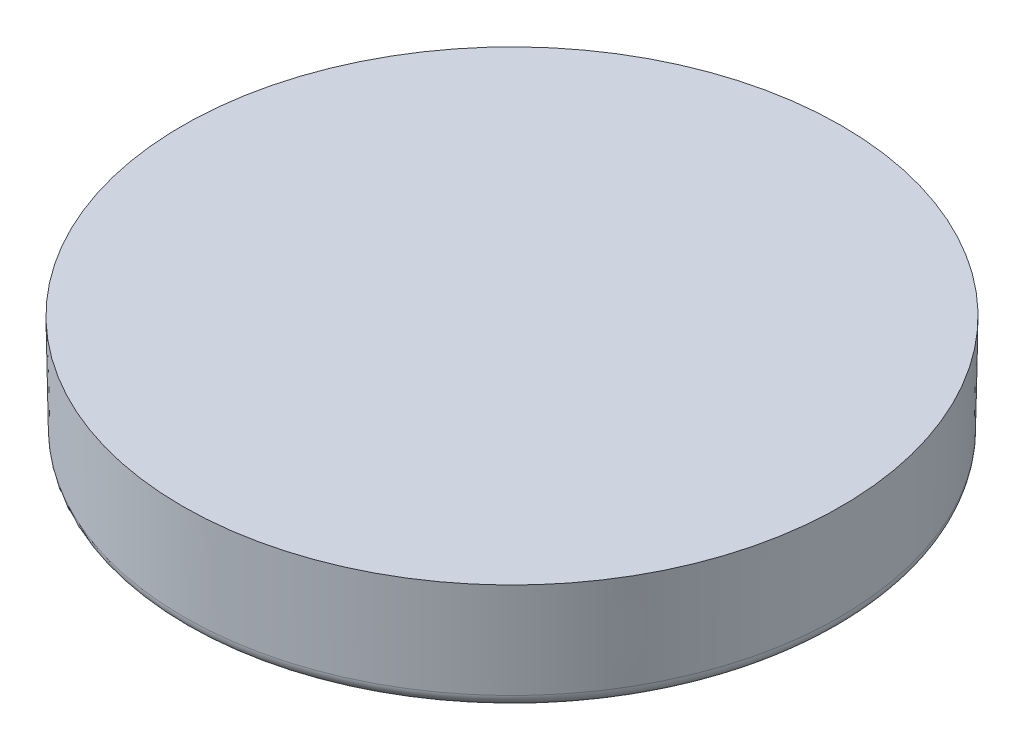
SolidWorks part; units mm, degrees
material "CA"
ref_plane "Front Plane" through (0, 0, 0) normal (0, 0, 1) x (1, 0, 0)
ref_plane "Top Plane" through (0, 0, 0) normal (0, 1, 0) x (1, 0, 0)
ref_plane "Right Plane" through (0, 0, 0) normal (1, 0, 0) x (0, 0, -1)
sketch "Sketch1" plane through (0, 0, 0) normal (0, 1, 0) x (1, 0, 0)
  circle A0 centre (0, 0) radius 19.05
  dimension "D1" = 38.1
extrude "Boss-Extrude1" add sketch "Sketch1" against normal blind 6.35 draft 1
sketch "Sketch6" plane through (0, 0, 0) normal (0, 0, 1) x (1, 0, 0)
  line L0 (0, 0) -> (0, -2.54) construction
  line L1 (0, -2.54) -> (-6.985, -9.525)
  line L2 (0, -2.54) -> (6.985, -9.525)
  line L3 (-6.985, -9.525) -> (6.985, -9.525)
  line L5 (19.05, 0) -> (-19.05, 0) construction
  dimension "D1" = 2.54
  dimension "D2" = 90
  dimension "D3" = 9.525
extrude "Cut-Extrude3" cut sketch "Sketch6" against normal through all
pattern_circular "CirPattern3" count 24 over 360 about axis through (0, 0, 0) along (0, 1, 0) of "Cut-Extrude3"
sketch "Sketch7" plane through (0, 0, 0) normal (0, 1, 0) x (1, 0, 0)
  circle A1 centre (0, 0) radius 19.05
  circle A2 centre (0, 0) radius 19.05
  circle A3 centre (0, 0) radius 16.637
  circle A4 centre (0, 0) radius 16.637
  dimension "D1" = 0
  dimension "D2" = 2.413
extrude "Boss-Extrude3" add sketch "Sketch7" against normal blind 6.35 draft 1
fillet "Fillet2" radius 0.762 2 edges at (0, -6.35, 18.9392) (0, -6.35, 16.7478)
sketch "Sketch11 - OFFSET .005" plane through (0, 0, 0) normal (0, 1, 0) x (1, 0, 0)
  circle A1 centre (0, 0) radius 19.177
  circle A2 centre (0, 0) radius 19.177
  dimension "D1" = 0.127
